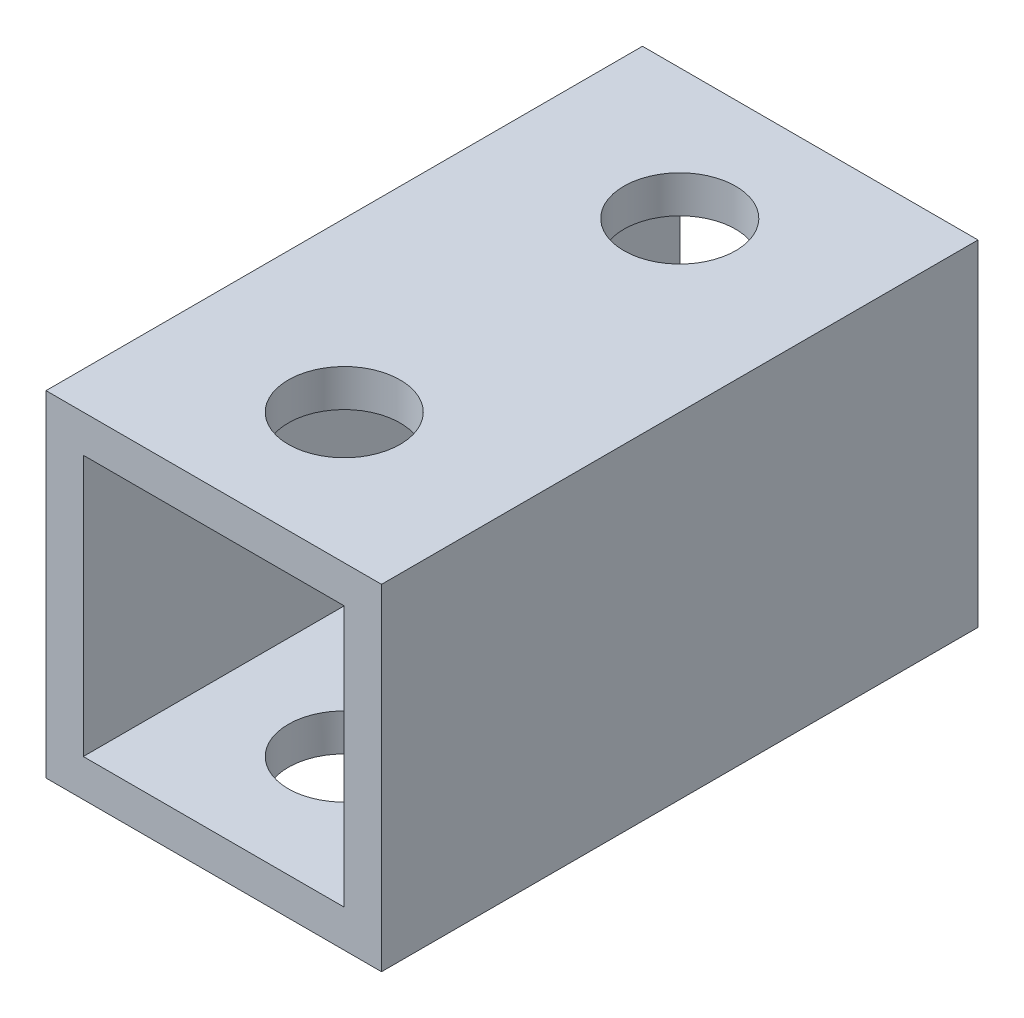
SolidWorks part; units mm, degrees
ref_plane "正面" through (0, 0, 0) normal (0, 0, 1) x (1, 0, 0)
ref_plane "平面" through (0, 0, 0) normal (0, 1, 0) x (1, 0, 0)
ref_plane "右側面" through (0, 0, 0) normal (1, 0, 0) x (0, 0, -1)
sketch "ｽｹｯﾁ1" plane through (0, 0, 0) normal (0, 0, 1) x (1, 0, 0)
  line L1 (-4.5, 4.5) -> (4.5, 4.5)
  line L2 (-4.5, 4.5) -> (-4.5, -4.5)
  line L3 (-4.5, -4.5) -> (4.5, -4.5)
  line L4 (4.5, 4.5) -> (4.5, -4.5)
  line L5 (-4.5, 4.5) -> (4.5, -4.5) construction
  line L6 (-4.5, -4.5) -> (4.5, 4.5) construction
  point P0 (0, 0)
  dimension "D1" = 9
  dimension "D2" = 9
extrude "ﾎﾞｽ - 押し出し1" add sketch "ｽｹｯﾁ1" along normal blind 16
sketch "ｽｹｯﾁ2" plane through (0, 0, 16) normal (0, 0, 1) x (1, 0, 0)
  line L1 (-3.5, 3.5) -> (3.5, 3.5)
  line L2 (-3.5, 3.5) -> (-3.5, -3.5)
  line L3 (-3.5, -3.5) -> (3.5, -3.5)
  line L4 (3.5, 3.5) -> (3.5, -3.5)
  line L5 (-3.5, 3.5) -> (3.5, -3.5) construction
  line L6 (-3.5, -3.5) -> (3.5, 3.5) construction
  point P0 (0, 0)
  dimension "D1" = 7
  dimension "D2" = 7
extrude "ｶｯﾄ - 押し出し1" cut sketch "ｽｹｯﾁ2" against normal blind 20
sketch "ｽｹｯﾁ3" plane through (0, 4.5, 0) normal (0, 1, 0) x (1, 0, 0)
  line L0 (0, 0) -> (0, -3.5)
  line L1 (0, -16) -> (0, -12.5)
  line L2 (4.5, -16) -> (-4.5, -16) construction
  circle A0 centre (0, -3.5) radius 1.5
  circle A1 centre (0, -12.5) radius 1.4996
  dimension "D3" = 3
  dimension "D4" = 2.9992
  dimension "D1" = 3.5
  dimension "D2" = 3.5
extrude "ｶｯﾄ - 押し出し2" cut sketch "ｽｹｯﾁ3" against normal blind 20
